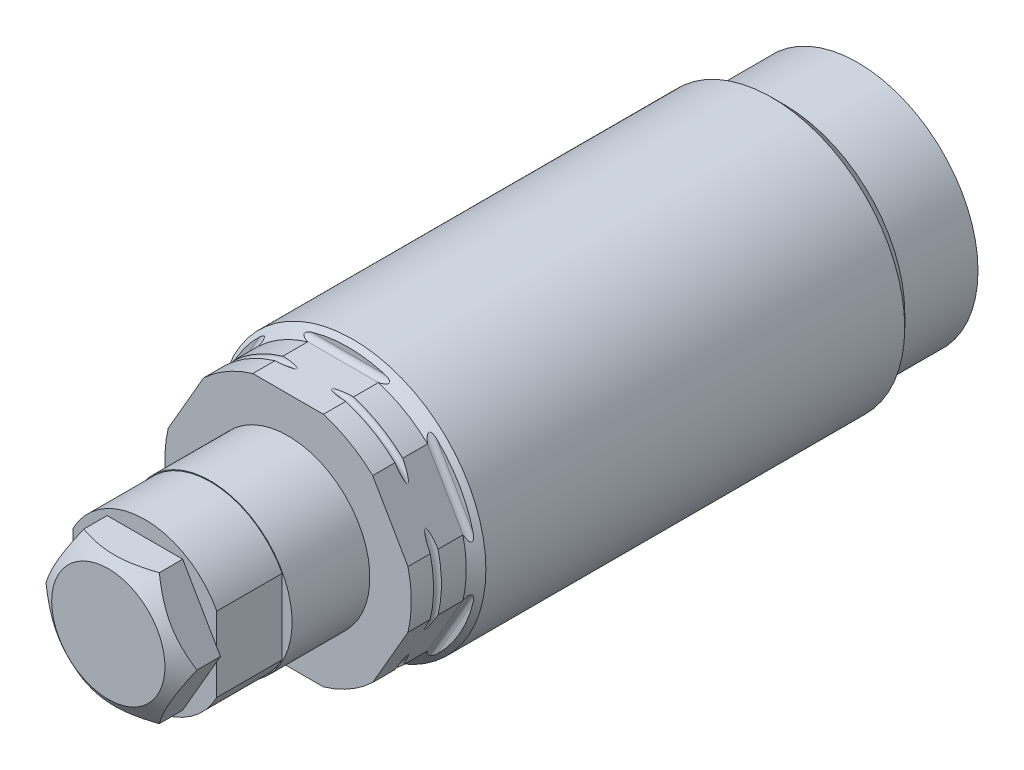
SolidWorks part; units mm, degrees
material "Alloy Steel"
ref_plane "Front Plane" through (0, 0, 0) normal (0, 0, 1) x (1, 0, 0)
ref_plane "Top Plane" through (0, 0, 0) normal (0, 1, 0) x (1, 0, 0)
ref_plane "Right Plane" through (0, 0, 0) normal (1, 0, 0) x (0, 0, -1)
sketch "Sketch1" plane through (0, 0, 0) normal (1, 0, 0) x (0, 0, -1)
  line L0 (0, 0) -> (122.3375, 0) construction
  line L1 (0, 0) -> (0, 11.6713)
  line L6 (0, 11.6713) -> (-7.112, 11.6713)
  line L7 (-7.112, 11.6713) -> (-8.3566, 12.9159)
  line L8 (-8.3566, 12.9159) -> (-49.0255, 12.9159)
  line L9 (-49.0255, 12.9159) -> (-49.978, 11.9634)
  line L10 (-49.978, 11.9634) -> (-55.312, 11.9634)
  line L11 (-55.312, 11.9634) -> (-55.312, 0)
  line L12 (0, 0) -> (-55.312, 0)
  dimension "D5" = 23.3426
  dimension "D6" = 7.112
  dimension "D7" = 25.8318
  dimension "D8" = 45
  dimension "D9" = 55.312
  dimension "D10" = 23.9268
  dimension "D11" = 45
  dimension "D12" = 5.334
revolve "Revolve1" add sketch "Sketch1" angle 360 about L0
sketch "Sketch2" plane through (0, 0, 0) normal (1, 0, 0) x (0, 0, -1)
  line L0 (0, 0) -> (-47.105, 0) construction
  line L1 (-55.312, 11.4617) -> (-49.978, 11.4617)
  line L2 (-55.312, 11.9634) -> (-55.312, -11.9634) construction
  line L3 (-49.47, 11.9697) -> (-49.47, 14.6367)
  line L4 (-49.47, 14.6367) -> (-55.312, 14.6367)
  line L5 (-55.312, 14.6367) -> (-55.312, 11.4617)
  arc A0 (-49.47, 11.9697) -> (-49.978, 11.4617) centre (-49.978, 11.9697) cw
  dimension "D4" = 0.508
  dimension "D1" = 22.9235
  dimension "D2" = 5.842
  dimension "D3" = 3.175
extrude "Cut-Extrude1" cut sketch "Sketch2" against normal through all and the other way through all
pattern_circular "CirPattern1" count 6 over 360 about axis through (0, 0, 0) along (0, 0, 1) of "Cut-Extrude1"
sketch "Sketch3" plane through (0, 0, 0) normal (1, 0, 0) x (0, 0, -1)
  line L0 (0, 0) -> (-60.8041, 0) construction
  line L1 (-72.771, 0) -> (-72.771, 7.9375) construction
  line L2 (-69.215, 7.9375) -> (-55.312, 7.9375)
  line L3 (-55.312, 2.7621) -> (-55.312, 8.6996) construction
  line L4 (-55.312, 7.9375) -> (-55.312, 0)
  line L5 (-55.312, 2.7621) -> (-55.312, -2.7621) construction
  line L6 (-55.312, 0) -> (-69.215, 0)
  line L7 (-69.215, 7.9375) -> (-69.215, 0)
  line L8 (0, -11.6713) -> (0, 11.6713) construction
  dimension "D1" = 3.556
  dimension "D2" = 15.875
  dimension "D3" = 72.771
revolve "Revolve2" add sketch "Sketch3" angle 360 about L0
sketch "Sketch4" plane through (0, 0, 69.215) normal (0, 0, 1) x (1, 0, 0)
  circle A0 centre (0, 0) radius 3.0226
  circle A1 centre (0, 0) radius 7.9375 construction
  dimension "D1" = 6.0452
extrude "Cut-Extrude2" cut sketch "Sketch4" against normal blind 8.001
sketch "Sketch5" plane through (0, 0, 0) normal (1, 0, 0) x (0, 0, -1)
  line L0 (-55.312, 11.4617) -> (-55.312, 8.6996) construction
  line L1 (0, 0) -> (-52.6213, 0) construction
  line L2 (-53.153, 15.1384) -> (-53.153, 11.9634)
  line L3 (-52.391, 15.1384) -> (-52.391, 11.9634)
  line L4 (-53.153, 15.1384) -> (-52.391, 15.1384)
  arc A0 (-53.153, 11.9634) -> (-52.391, 11.9634) centre (-52.772, 11.9634) ccw
  dimension "D3" = 0.762
  dimension "D1" = 2.54
  dimension "D2" = 11.9634
  dimension "D4" = 3.175
revolve "Cut-Revolve1" cut sketch "Sketch5" angle 360 about L1
sketch "Sketch10" plane through (0, 0, 0) normal (0, 1, 0) x (1, 0, 0)
  line L0 (0, 0) -> (0, -56.3853) construction
  line L1 (7.9375, -69.215) -> (7.9375, -55.312) construction
  line L2 (6.9723, -69.215) -> (7.9375, -69.215)
  line L3 (6.9723, -69.215) -> (6.9723, -62.865)
  line L4 (6.9723, -62.865) -> (7.9375, -62.865)
  line L5 (7.9375, -69.215) -> (7.9375, -62.865)
  line L6 (-7.9375, -69.215) -> (7.9375, -69.215) construction
  line L7 (-7.9375, -69.215) -> (-7.9375, -62.865)
  line L8 (-6.9723, -62.865) -> (-7.9375, -62.865)
  line L9 (-6.9723, -69.215) -> (-6.9723, -62.865)
  line L10 (-6.9723, -69.215) -> (-7.9375, -69.215)
  dimension "D1" = 13.9446
  dimension "D2" = 6.35
extrude "Cut-Extrude3" cut sketch "Sketch10" against normal through all and the other way through all
sketch "Sketch11" plane through (0, 0, 69.215) normal (0, 0, 1) x (1, 0, 0)
  line L1 (3.6662, 6.35) -> (-3.6662, 6.35)
  line L2 (-3.6662, 6.35) -> (-7.3323, 0)
  line L3 (-7.3323, 0) -> (-3.6662, -6.35)
  line L4 (-3.6662, -6.35) -> (3.6662, -6.35)
  line L5 (3.6662, -6.35) -> (7.3323, 0)
  line L6 (7.3323, 0) -> (3.6662, 6.35)
  circle A0 centre (0, 0) radius 6.35 construction
  dimension "D1" = 12.7
extrude "Extrude2" add sketch "Sketch11" along normal blind 3.556
sketch "Sketch12" plane through (0, 0, 0) normal (0, 1, 0) x (1, 0, 0)
  line L0 (-7.3323, -71.4873) -> (-7.3323, -72.771)
  line L1 (-7.3323, -72.771) -> (-7.3323, -69.215) construction
  line L2 (-7.3323, -72.771) -> (-5.4991, -72.771)
  line L3 (-3.6662, -72.771) -> (-7.3323, -72.771) construction
  line L4 (-5.4991, -72.771) -> (-7.3323, -71.4873)
  line L5 (0, 0) -> (0, -66.9815) construction
  dimension "D1" = 35
  dimension "D2" = 10.9982
revolve "Cut-Revolve3" cut sketch "Sketch12" angle 360 about L5
sketch "Sketch13" plane through (0, 0, 0) normal (1, 0, 0) x (0, 0, -1)
  line L0 (0, 0) -> (-72.771, 0) construction
  line L1 (-72.771, 5.4991) -> (-72.771, -5.4991) construction
  line L2 (-69.215, 7.86) -> (-62.865, 7.86)
  line L3 (-69.215, 7.9375) -> (-69.215, 3.7935) construction
  line L4 (-62.865, 7.86) -> (-62.865, 7.9375)
  line L5 (-55.312, 7.9375) -> (-69.215, 7.9375) construction
  line L6 (-62.865, 7.9375) -> (-69.215, 7.9375)
  line L7 (-69.215, 7.9375) -> (-69.215, 7.86)
  dimension "D1" = 6.35
  dimension "D2" = 15.72
revolve "Cut-Revolve4" cut sketch "Sketch13" angle 360 about L0
